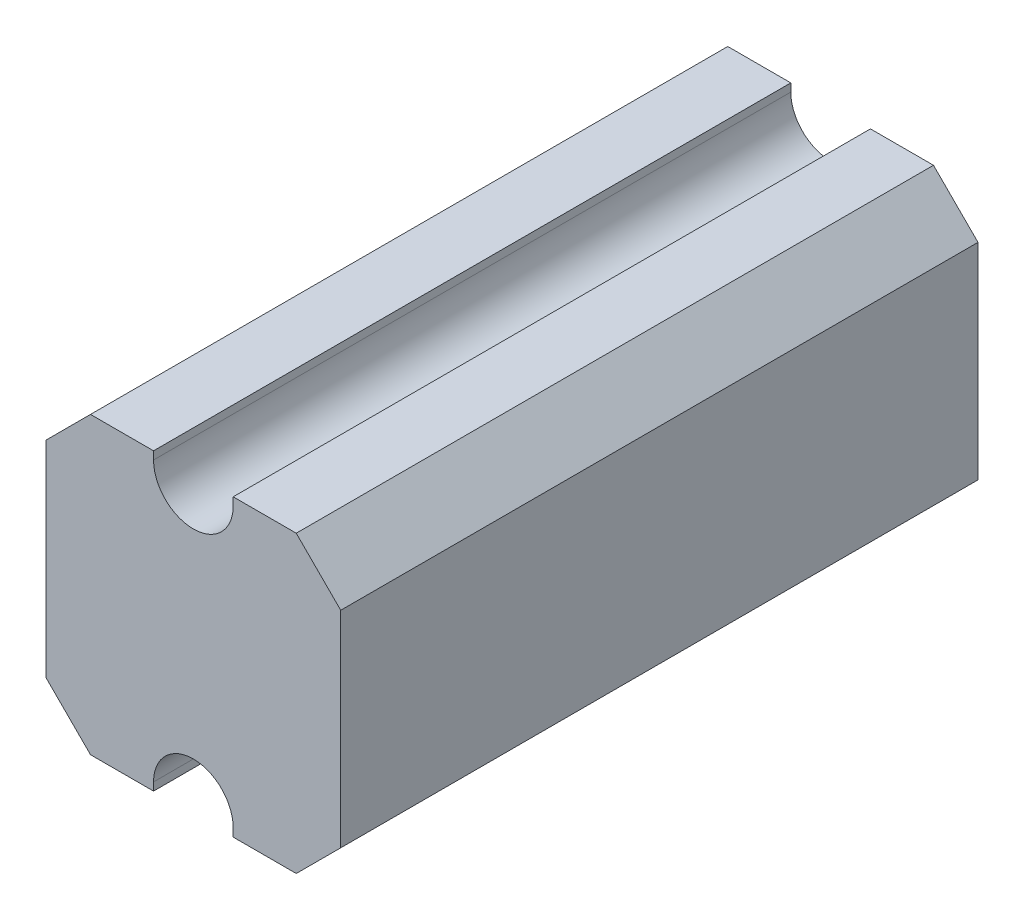
SolidWorks part; units mm, degrees
ref_plane "Front Plane" through (0, 0, 0) normal (0, 0, 1) x (1, 0, 0)
ref_plane "Top Plane" through (0, 0, 0) normal (0, 1, 0) x (1, 0, 0)
ref_plane "Right Plane" through (0, 0, 0) normal (1, 0, 0) x (0, 0, -1)
sketch "Sketch1" plane through (0, 0, 0) normal (0, 0, 1) x (1, 0, 0)
  line L0 (-175, 0) -> (175, 0) construction
  line L1 (175, -125) -> (175, 125) construction
  line L2 (-175, -125) -> (-175, 125) construction
  line L3 (-175, 125) -> (-125, 175) construction
  line L4 (-125, 175) -> (-50, 175) construction
  line L5 (0, 0) -> (0, 175) construction
  line L6 (175, 125) -> (125, 175) construction
  line L7 (125, 175) -> (50, 175) construction
  line L8 (-175, -125) -> (-125, -175) construction
  line L9 (-125, -175) -> (-50, -175) construction
  line L10 (175, -125) -> (125, -175) construction
  line L11 (125, -175) -> (50, -175) construction
  line L12 (-185, -129.1421) -> (-129.1421, -185)
  line L13 (-129.1421, -185) -> (-38.7298, -185)
  line L14 (129.1421, -185) -> (38.7298, -185)
  line L15 (185, -129.1421) -> (129.1421, -185)
  line L16 (185, -129.1421) -> (185, 129.1421)
  line L17 (185, 129.1421) -> (129.1421, 185)
  line L18 (129.1421, 185) -> (38.7298, 185)
  line L19 (-129.1421, 185) -> (-38.7298, 185)
  line L20 (-185, 129.1421) -> (-129.1421, 185)
  line L21 (-185, -129.1421) -> (-185, 129.1421)
  line L22 (-50, 175) -> (-50, 185)
  line L23 (50, 175) -> (50, 185)
  line L24 (50, -175) -> (50, -185)
  line L25 (-50, -175) -> (-50, -185)
  arc A0 (-50, 175) -> (50, 175) centre (0, 175) ccw
  arc A1 (-50, -175) -> (50, -175) centre (0, -175) cw
  arc A2 (-38.7298, -185) -> (38.7298, -185) centre (0, -175) cw
  arc A3 (-38.7298, 185) -> (38.7298, 185) centre (0, 175) ccw
  point P4 (0, 0)
  point P8 (175, 0)
  point P11 (-175, 0)
  dimension "D2" = 350
  dimension "D5" = 50
  dimension "D1" = 350
  dimension "D3" = 50
  dimension "D4" = 50
  dimension "D6" = 10
extrude "Boss-Extrude1" add sketch "Sketch1" against normal blind 800 contours L25 A1 L24 L14 L15 L16 L17 L18 L23 A0 L22 L19 L20 L21 L12 L13
